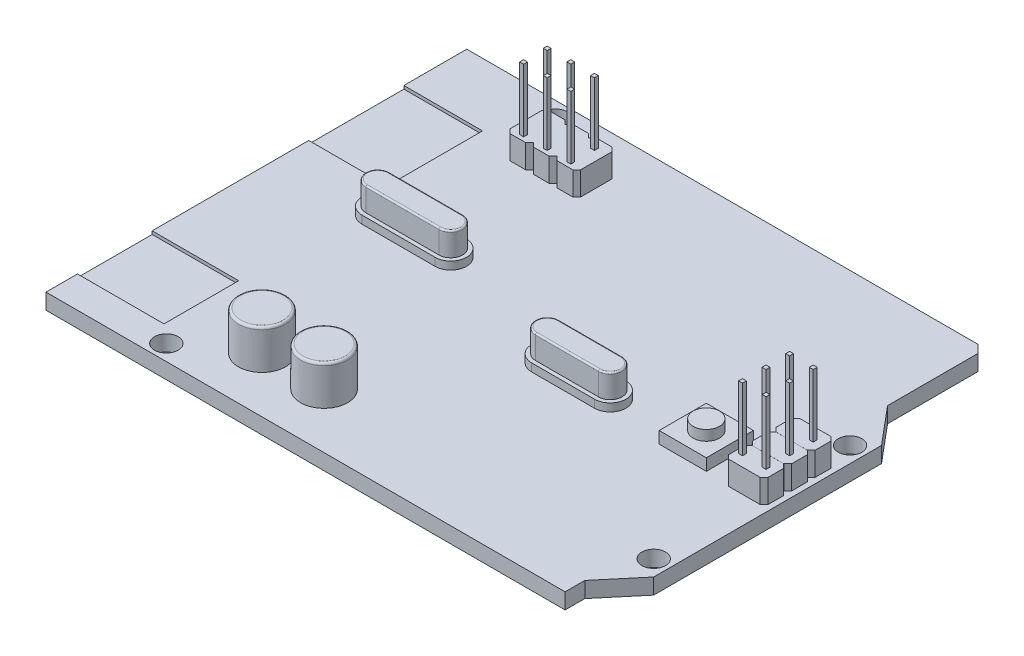
SolidWorks part; units mm, degrees
ref_plane "Front Plane" through (0, 0, 0) normal (0, 0, 1) x (1, 0, 0)
ref_plane "Top Plane" through (0, 0, 0) normal (0, 1, 0) x (1, 0, 0)
ref_plane "Right Plane" through (0, 0, 0) normal (1, 0, 0) x (0, 0, -1)
sketch "Sketch1" plane through (0, 0, 0) normal (0, 1, 0) x (1, 0, 0)
  line L0 (0, 0) -> (0, 53.5)
  line L1 (0, 53.5) -> (65, 53.5)
  line L2 (66, 52.5) -> (66, 41)
  line L3 (66, 41) -> (70, 36.233)
  line L4 (70, 36.233) -> (70, 7.267)
  line L5 (70, 7.267) -> (66, 2.5)
  line L6 (66, 2.5) -> (66, 0)
  line L7 (66, 0) -> (0, 0)
  line L8 (65, 53.5) -> (66, 52.5)
  point P4 (66, 53.5)
  dimension "D1" = 12.5
  dimension "D2" = 2.5
  dimension "D3" = 4
  dimension "D4" = 53.5
  dimension "D5" = 140
  dimension "D6" = 66
extrude "Boss-Extrude1" add sketch "Sketch1" along normal blind 2
sketch "Sketch2" plane through (0, 2, 0) normal (0, 1, 0) x (1, 0, 0)
  line L0 (0, 53.5) -> (0, 0) construction
  line L1 (65, 53.5) -> (0, 53.5) construction
  line L2 (0, 0) -> (66, 0) construction
  line L3 (70, 7.267) -> (70, 36.233) construction
  circle A0 centre (68, 34.233) radius 1.5
  circle A1 centre (68, 9.267) radius 1.5
  circle A2 centre (13.3, 2) radius 1.5
  circle A3 centre (13.3, 51.5) radius 1.5
  dimension "D1" = 3
  dimension "D2" = 13.3
  dimension "D3" = 13.3
  dimension "D4" = 2
  dimension "D5" = 2
  dimension "D6" = 2
  dimension "D7" = 2
  dimension "D8" = 2
  dimension "D9" = 2
extrude "Cut-Extrude1" cut sketch "Sketch2" against normal through all
sketch "Sketch3" plane through (0, 2, 0) normal (0, 1, 0) x (1, 0, 0)
  line L0 (0, 53.5) -> (0, 0) construction
  line L1 (0, 13.5) -> (11, 13.5)
  line L2 (0, 13.5) -> (0, 4)
  line L3 (0, 4) -> (11, 4)
  line L4 (11, 13.5) -> (11, 4)
  line L5 (65, 53.5) -> (0, 53.5) construction
  line L6 (0, 45.5) -> (10, 45.5)
  line L7 (0, 45.5) -> (0, 33.4)
  line L8 (0, 33.4) -> (10, 33.4)
  line L9 (10, 45.5) -> (10, 33.4)
  line L10 (0, 0) -> (66, 0) construction
  dimension "D1" = 12.1
  dimension "D2" = 10
  dimension "D3" = 8
  dimension "D4" = 11
  dimension "D5" = 9.5
  dimension "D6" = 4
extrude "Cut-Extrude3" cut sketch "Sketch3" against normal blind 0.4
sketch "Sketch6" plane through (0, 2, 0) normal (0, 1, 0) x (1, 0, 0)
  line L0 (65, 53.5) -> (0, 53.5) construction
  line L1 (64.8, 31) -> (68.8, 31)
  line L2 (64.3, 30.5) -> (64.3, 28.5048)
  line L3 (64.8, 28.0048) -> (68.8, 28.0048)
  line L4 (69.3, 30.5) -> (69.3, 28.5048)
  line L5 (70, 7.267) -> (70, 36.233) construction
  line L6 (64.3, 30.5) -> (64.8, 31)
  line L7 (64.3, 28.5048) -> (64.8, 28.0048)
  line L8 (68.8, 28.0048) -> (69.3, 28.5048)
  line L9 (68.8, 31) -> (69.3, 30.5)
  point P0 (64.3, 31)
  point P1 (69.3, 28.0048)
  point P2 (64.3, 28.0048)
  point P3 (69.3, 31)
  dimension "D1" = 22.5
  dimension "D2" = 5
  dimension "D3" = 2.9952
  dimension "D4" = 0.7
extrude "Boss-Extrude4" add sketch "Sketch6" along normal blind 3
pattern_linear "LPattern2" count 3 spacing 3 along (0, 0, 1) of "Boss-Extrude4"
sketch "Sketch7" plane through (0, 5, 0) normal (0, 1, 0) x (1, 0, 0)
  line L0 (68.8, 31) -> (64.8, 31) construction
  line L1 (64.8, 29.75) -> (65.3, 29.75)
  line L2 (64.8, 29.75) -> (64.8, 29.25)
  line L3 (64.8, 29.25) -> (65.3, 29.25)
  line L4 (65.3, 29.75) -> (65.3, 29.25)
  line L5 (64.3, 30.5) -> (64.3, 28.5048) construction
  dimension "D1" = 0.5
  dimension "D2" = 0.5
  dimension "D3" = 1.25
  dimension "D4" = 0.5
extrude "Boss-Extrude6" add sketch "Sketch7" along normal blind 8
pattern_linear "LPattern3" count 3 spacing 3 along (0, 0, 1) count 2 spacing 3 along (1, 0, 0) of "Boss-Extrude6"
sketch "Sketch9" plane through (0, 2, 0) normal (0, 1, 0) x (1, 0, 0)
  line L0 (14.5188, 48.4588) -> (15.0188, 48.9588)
  line L1 (15.0188, 48.9588) -> (17.0188, 48.9588)
  line L2 (14.5188, 48.4588) -> (14.5188, 44.4588)
  line L3 (15.0188, 43.9588) -> (17.0188, 43.9588)
  line L4 (17.5188, 48.4588) -> (17.5188, 44.4588)
  line L5 (17.0188, 48.9588) -> (17.5188, 48.4588)
  line L6 (17.0188, 43.9588) -> (17.5188, 44.4588)
  line L7 (14.5188, 44.4588) -> (15.0188, 43.9588)
  point P0 (14.5188, 48.9588)
  point P1 (17.5188, 43.9588)
  point P2 (14.5188, 43.9588)
  point P3 (17.5188, 48.9588)
  dimension "D1" = 3
  dimension "D2" = 5
extrude "Boss-Extrude8" add sketch "Sketch9" along normal blind 3
pattern_linear "LPattern4" count 3 spacing 3 along (1, 0, 0) of "Boss-Extrude8"
sketch "Sketch10" plane through (0, 5, 0) normal (0, 1, 0) x (1, 0, 0)
  line L0 (15.0188, 43.9588) -> (17.0188, 43.9588) construction
  line L1 (15.7688, 44.9588) -> (16.2688, 44.9588)
  line L2 (15.7688, 44.9588) -> (15.7688, 44.4588)
  line L3 (15.7688, 44.4588) -> (16.2688, 44.4588)
  line L4 (16.2688, 44.9588) -> (16.2688, 44.4588)
  line L5 (14.5188, 48.4588) -> (14.5188, 44.4588) construction
  dimension "D1" = 0.5
  dimension "D2" = 0.5
  dimension "D3" = 0.5
  dimension "D4" = 1.25
extrude "Boss-Extrude9" add sketch "Sketch10" along normal blind 8
pattern_linear "LPattern6" count 3 spacing 3 along (1, 0, 0) count 2 spacing 3 along (0, 0, -1) of "Boss-Extrude9"
sketch "Sketch11" plane through (0, 2, 0) normal (0, 1, 0) x (1, 0, 0)
  line L1 (61.7174, 22.2407) -> (55.7174, 22.2407)
  line L2 (61.7174, 22.2407) -> (61.7174, 28.2407)
  line L3 (61.7174, 28.2407) -> (55.7174, 28.2407)
  line L4 (55.7174, 22.2407) -> (55.7174, 28.2407)
  dimension "D1" = 6
extrude "Boss-Extrude10" add sketch "Sketch11" along normal blind 1.5
sketch "Sketch12" plane through (0, 3.5, 0) normal (0, 1, 0) x (1, 0, 0)
  circle A0 centre (58.7174, 25.2407) radius 1.6805
extrude "Boss-Extrude11" add sketch "Sketch12" along normal blind 1.3
sketch "Sketch15" plane through (0, 2, 0) normal (0, 1, 0) x (1, 0, 0)
  line L0 (39.658, 24.0834) -> (47.658, 24.0834) construction
  line L1 (39.658, 26.0834) -> (47.658, 26.0834)
  line L2 (39.658, 22.0834) -> (47.658, 22.0834)
  arc A0 (39.658, 26.0834) -> (39.658, 22.0834) centre (39.658, 24.0834) ccw
  arc A1 (47.658, 22.0834) -> (47.658, 26.0834) centre (47.658, 24.0834) ccw
  point P2 (43.658, 24.0834)
  dimension "D1" = 8
  dimension "D2" = 4
extrude "Boss-Extrude13" add sketch "Sketch15" along normal blind 1
sketch "Sketch26" plane through (0, 3, 0) normal (0, 1, 0) x (1, 0, 0)
  line L0 (39.658, 24.0834) -> (47.658, 24.0834) construction
  line L1 (39.658, 25.5834) -> (47.658, 25.5834)
  line L2 (39.658, 22.5834) -> (47.658, 22.5834)
  arc A0 (39.658, 25.5834) -> (39.658, 22.5834) centre (39.658, 24.0834) ccw
  arc A1 (47.658, 22.5834) -> (47.658, 25.5834) centre (47.658, 24.0834) ccw
  arc A2 (39.658, 26.0834) -> (39.658, 22.0834) centre (39.658, 24.0834) ccw construction
  point P4 (43.658, 24.0834)
  dimension "D1" = 1.5
extrude "Boss-Extrude14" add sketch "Sketch26" along normal blind 3
fillet "Fillet1" radius 0.2 4 edges at (43.658, 6, -25.5834) (49.158, 6, -24.0834) (43.658, 6, -22.5834) (38.158, 6, -24.0834)
sketch "Sketch27" plane through (0, 2, 0) normal (0, 1, 0) x (1, 0, 0)
  line L0 (12.6077, 29.5689) -> (21.9004, 29.5689) construction
  line L1 (12.6077, 31.5689) -> (21.9004, 31.5689)
  line L2 (12.6077, 27.5689) -> (21.9004, 27.5689)
  arc A0 (12.6077, 31.5689) -> (12.6077, 27.5689) centre (12.6077, 29.5689) ccw
  arc A1 (21.9004, 27.5689) -> (21.9004, 31.5689) centre (21.9004, 29.5689) ccw
  arc A2 (47.658, 22.0834) -> (47.658, 26.0834) centre (47.658, 24.0834) ccw construction
  point P2 (17.2541, 29.5689)
extrude "Boss-Extrude15" add sketch "Sketch27" along normal blind 1
sketch "Sketch28" plane through (0, 3, 0) normal (0, 1, 0) x (1, 0, 0)
  line L0 (12.6077, 29.5689) -> (21.9004, 29.5689) construction
  line L1 (12.6077, 31.0689) -> (21.9004, 31.0689)
  line L2 (12.6077, 28.0689) -> (21.9004, 28.0689)
  arc A0 (12.6077, 31.0689) -> (12.6077, 28.0689) centre (12.6077, 29.5689) ccw
  arc A1 (21.9004, 28.0689) -> (21.9004, 31.0689) centre (21.9004, 29.5689) ccw
  arc A2 (12.6077, 31.5689) -> (12.6077, 27.5689) centre (12.6077, 29.5689) ccw construction
  point P4 (17.2541, 29.5689)
  dimension "D1" = 0.5
extrude "Boss-Extrude16" add sketch "Sketch28" along normal blind 3
fillet "Fillet2" radius 0.2 4 edges at (17.2541, 6, -31.0689) (23.4004, 6, -29.5689) (17.2541, 6, -28.0689) (11.1077, 6, -29.5689)
sketch "Sketch29" plane through (0, 2, 0) normal (0, 1, 0) x (1, 0, 0)
  line L0 (0, 0) -> (66, 0) construction
  circle A0 centre (20.4575, 7) radius 3
  circle A1 centre (28.3577, 7) radius 3
  dimension "D1" = 6
  dimension "D2" = 6
  dimension "D3" = 7
  dimension "D4" = 7
extrude "Boss-Extrude17" add sketch "Sketch29" along normal blind 5
fillet "Fillet3" radius 0.3 2 edges at (20.4575, 7, -4) (28.3577, 7, -4)
sketch "Sketch31" plane through (0, 2, 0) normal (0, 1, 0) x (1, 0, 0)
  text T0 "MADE BY MAJD AF" font "Century Gothic" height 3.5
